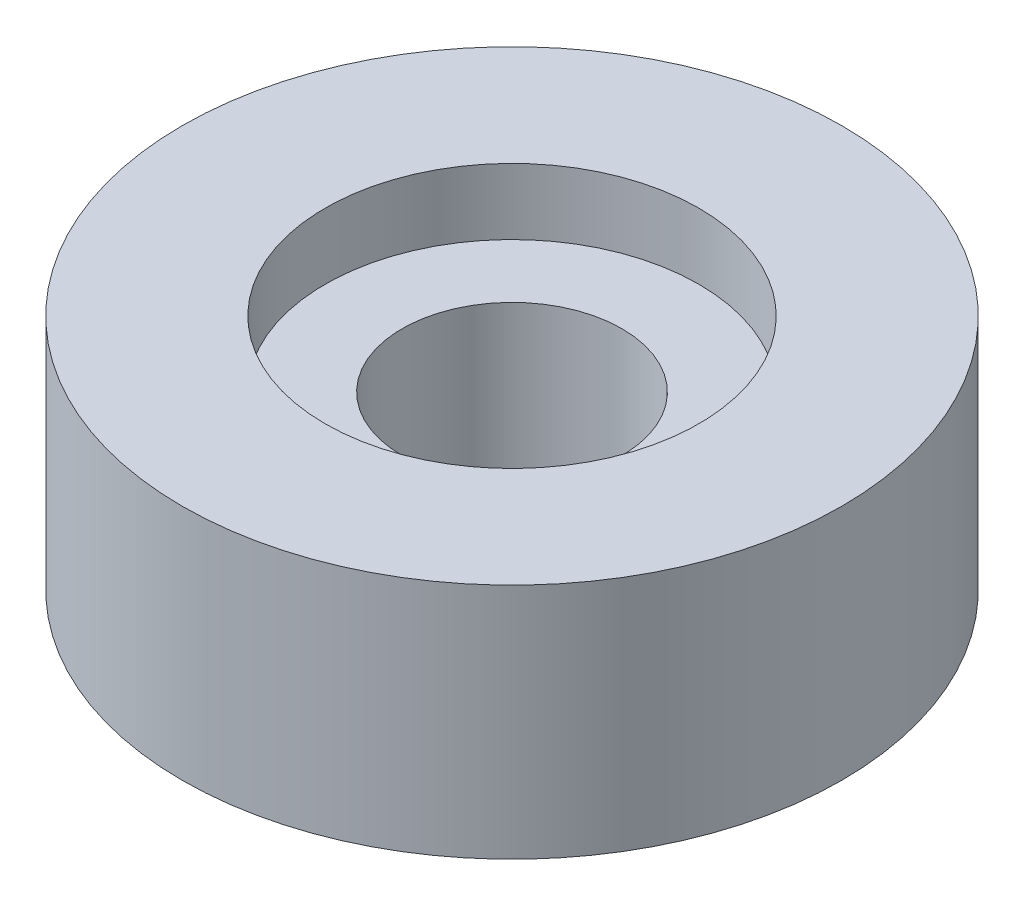
SolidWorks part; units mm, degrees
ref_plane "Front" through (0, 0, 0) normal (0, 0, 1) x (1, 0, 0)
ref_plane "Top" through (0, 0, 0) normal (0, 1, 0) x (1, 0, 0)
ref_plane "Right" through (0, 0, 0) normal (1, 0, 0) x (0, 0, -1)
sketch "Sketch1" plane through (0, 0, 0) normal (0, 1, 0) x (1, 0, 0)
  circle A0 centre (0, 0) radius 2.5
  circle A1 centre (0, 0) radius 7.5
  dimension "D1" = 5
  dimension "D2" = 15
extrude "Boss-Extrude1" add sketch "Sketch1" along normal blind 3.9
sketch "Sketch2" plane through (0, 3.9, 0) normal (0, 1, 0) x (1, 0, 0)
  circle A0 centre (0, 0) radius 4.25
  circle A1 centre (0, 0) radius 7.5
  circle A2 centre (0, 0) radius 7.5 construction
  dimension "D1" = 8.5
extrude "Boss-Extrude2" add sketch "Sketch2" along normal blind 1.5
